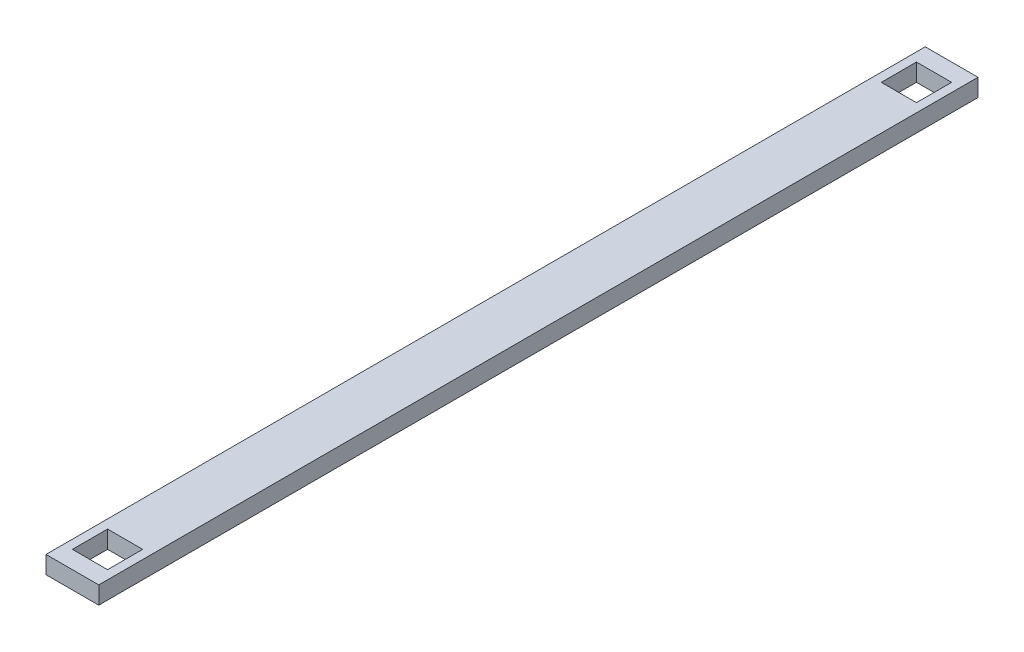
SolidWorks part; units mm, degrees
material "BUTYL"
ref_plane "Plano frontal" through (0, 0, 0) normal (0, 0, 1) x (1, 0, 0)
ref_plane "Plano superior" through (0, 0, 0) normal (0, 1, 0) x (1, 0, 0)
ref_plane "Plano direito" through (0, 0, 0) normal (1, 0, 0) x (0, 0, -1)
sketch "Esboço1" plane through (0, 0, 0) normal (0, 0, 1) x (1, 0, 0)
  line L1 (0, 0) -> (3, 0)
  line L2 (0, 0) -> (0, 1)
  line L3 (0, 1) -> (3, 1)
  line L4 (3, 0) -> (3, 1)
  dimension "D1" = 1
  dimension "D2" = 3
  dimension "D3" = 3
extrude "Ressalto-extrusão1" add sketch "Esboço1" against normal blind 50
sketch "Esboço3" plane through (0, 1, 0) normal (0, 1, 0) x (1, 0, 0)
  line L0 (3, 0) -> (0, 0) construction
  line L1 (0.5, 3) -> (2.5, 3)
  line L2 (0.5, 3) -> (0.5, 1)
  line L3 (0.5, 1) -> (2.5, 1)
  line L4 (2.5, 3) -> (2.5, 1)
  line L15 (0, 50) -> (0, 0) construction
  line L26 (0, 25) -> (3, 25) construction
  line L27 (3, 50) -> (3, 0) construction
  line L40 (2.5, 47) -> (2.5, 49)
  line L41 (0.5, 49) -> (2.5, 49)
  line L42 (0.5, 47) -> (0.5, 49)
  line L43 (0.5, 47) -> (2.5, 47)
  dimension "D1" = 0.5
  dimension "D2" = 2
  dimension "D3" = 2
  dimension "D7" = 1
extrude "Corte-extrusão1" cut sketch "Esboço3" against normal blind 44
